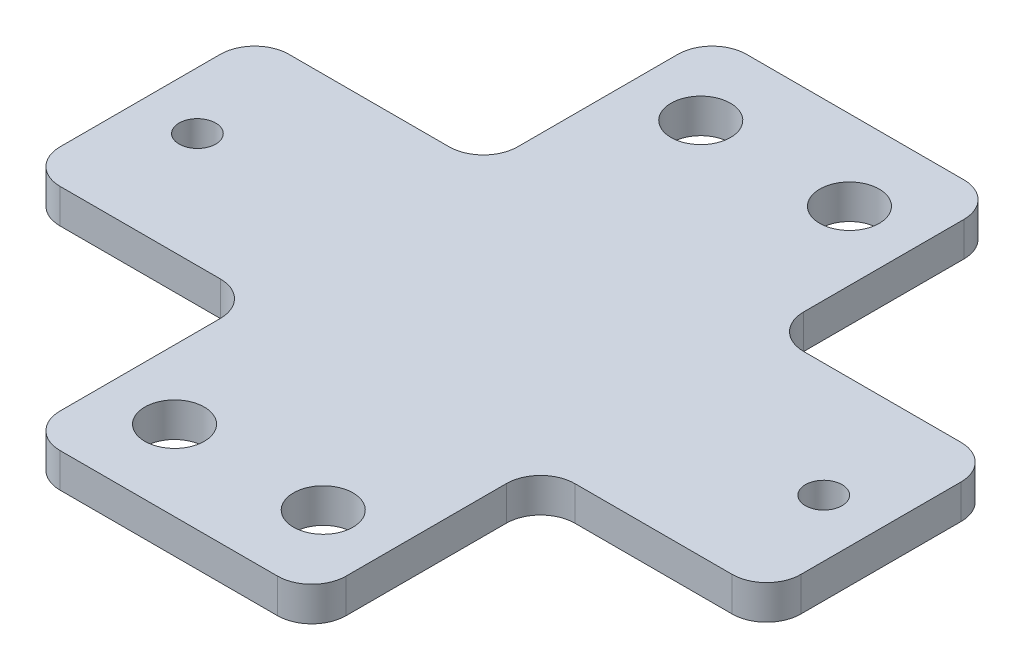
SolidWorks part; units mm, degrees
material "A-玻璃纤维"
ref_plane "前视基准面" through (0, 0, 0) normal (0, 0, 1) x (1, 0, 0)
ref_plane "上视基准面" through (0, 0, 0) normal (0, 1, 0) x (1, 0, 0)
ref_plane "右视基准面" through (0, 0, 0) normal (1, 0, 0) x (0, 0, -1)
sketch "草图1" plane through (0, 0, 0) normal (0, 1, 0) x (1, 0, 0)
  line L0 (0, 30) -> (25, 30) construction
  line L1 (0, 0) -> (25, 0)
  line L2 (0, 0) -> (0, 60)
  line L3 (0, 60) -> (25, 60)
  line L4 (25, 0) -> (25, 60)
  line L5 (12.5, 0) -> (12.5, 7) construction
  line L6 (12.5, 7) -> (6, 7) construction
  circle A0 centre (6, 7) radius 2.6
  circle A1 centre (19, 7) radius 2.6
  circle A2 centre (6, 53) radius 2.6
  circle A3 centre (19, 53) radius 2.6
  dimension "D3" = 13
  dimension "D4" = 5.2
  dimension "D5" = 46
  dimension "D1" = 60
  dimension "D2" = 25
extrude "凸台-拉伸1" add sketch "草图1" along normal blind 3
sketch "草图2" plane through (0, 3, 0) normal (0, 1, 0) x (1, 0, 0)
  line L0 (0, 30) -> (-20, 30) construction
  line L1 (0, 60) -> (0, 0) construction
  line L2 (12.5, 0) -> (12.5, 34.5436) construction
  line L3 (0, 40) -> (-20, 40)
  line L4 (0, 40) -> (0, 20)
  line L5 (0, 20) -> (-20, 20)
  line L6 (-20, 40) -> (-20, 20)
  line L7 (0, 0) -> (25, 0) construction
  line L8 (25, 20) -> (44.75, 20)
  line L9 (44.75, 40) -> (44.75, 20)
  line L10 (25, 40) -> (44.75, 40)
  line L11 (25, 40) -> (25, 20)
  line L12 (39.75, 30) -> (12.5, 30) construction
  line L13 (25, 0) -> (25, 60) construction
  circle A0 centre (-15, 30) radius 1.6
  circle A1 centre (39.75, 30) radius 1.6
  dimension "D3" = 3.2
  dimension "D4" = 5
  dimension "D6" = 5
  dimension "D1" = 20
  dimension "D2" = 20
  dimension "D5" = 20
  dimension "D7" = 19.75
extrude "凸台-拉伸2" add sketch "草图2" against normal up to surface (3 mm away) up to face at (6, 0, -55.6)
fillet "圆角1" radius 3 12 edges at (25, 1.5, -20) (44.75, 1.5, -20) (44.75, 1.5, -40) (25, 1.5, -40) (25, 1.5, -60) (0, 1.5, -60) (0, 1.5, -40) (-20, 1.5, -40) (-20, 1.5, -20) (0, 1.5, -20) (0, 1.5, 0) (25, 1.5, 0)
